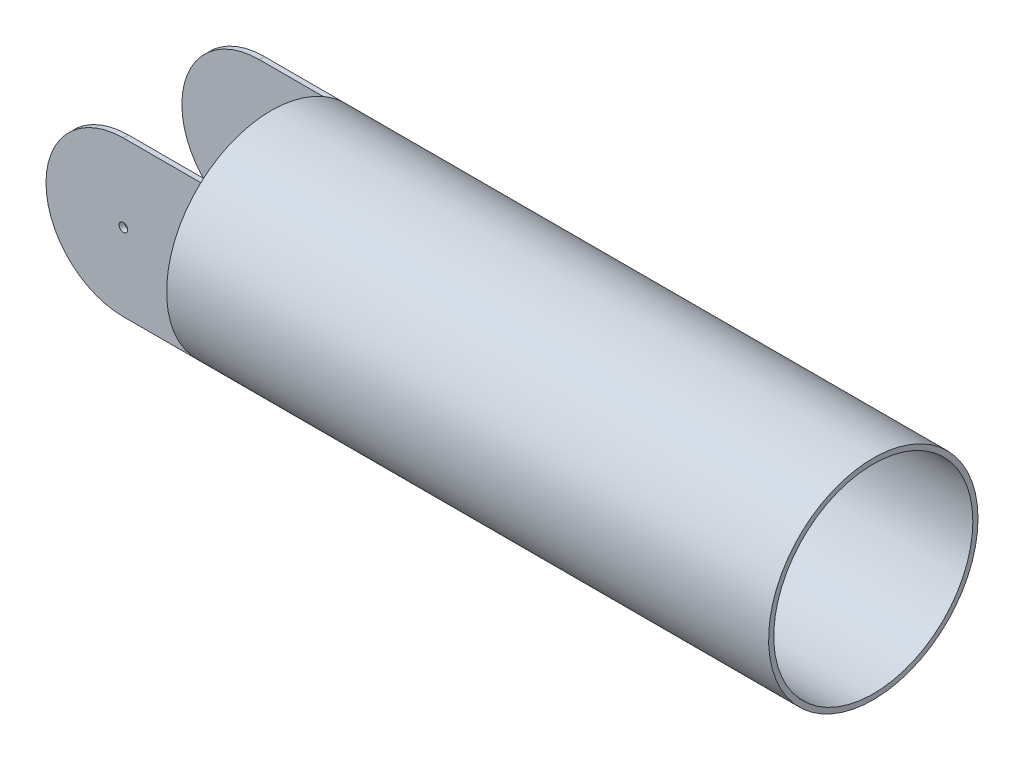
SolidWorks part; units mm, degrees
ref_plane "Ön Düzlem" through (0, 0, 0) normal (0, 0, 1) x (1, 0, 0)
ref_plane "Üst Düzlem" through (0, 0, 0) normal (0, 1, 0) x (1, 0, 0)
ref_plane "Sağ Düzlem" through (0, 0, 0) normal (1, 0, 0) x (0, 0, -1)
sketch "Çizim1" plane through (0, 0, 0) normal (0, 0, 1) x (1, 0, 0)
  line L1 (0, 0) -> (180, 0)
  line L2 (0, 0) -> (0, 180)
  line L3 (0, 180) -> (180, 180)
  line L4 (180, 0) -> (180, 180)
  dimension "D1" = 180
  dimension "D2" = 180
extrude "Yükseklik-Ekstrüzyon1" add sketch "Çizim1" along normal blind 164
sketch "Çizim3" plane through (180, 0, 0) normal (1, 0, 0) x (0, 0, -1)
  circle A0 centre (-82, 90) radius 121.7539
extrude "Yükseklik-Ekstrüzyon2" add sketch "Çizim3" along normal blind 700
sketch "Çizim4" plane through (0, 0, 164) normal (0, 0, 1) x (1, 0, 0)
  line L0 (90, 180) -> (0, 180)
  line L1 (0, 180) -> (0, 0)
  line L2 (0, 0) -> (90, 0)
  circle A0 centre (90, 90) radius 90
  line M1 (0, 180) -> (0, 0)
  line M2 (0, 0) -> (180, 0)
  line M4 (180, 180) -> (0, 180)
extrude "Kes-Ekstrüzyon1" cut sketch "Çizim4" against normal blind 700 contours A0 M4 M1 | A0 L1 M2
sketch "Çizim5" plane through (0, 180, 0) normal (0, 1, 0) x (1, 0, 0)
  line L0 (180, 0) -> (180, -164) construction
  line L1 (180, -6) -> (0, -6)
  line L2 (180, -6) -> (180, -158)
  line L3 (180, -158) -> (0, -158)
  line L4 (0, -6) -> (0, -158)
  line L5 (0, 0) -> (0, -164) construction
  line L6 (180, 0) -> (90, 0) construction
  line L7 (180, -164) -> (90, -164) construction
  dimension "D1" = 6
  dimension "D2" = 6
extrude "Kes-Ekstrüzyon2" cut sketch "Çizim5" against normal blind 700
sketch "Çizim6" plane through (0, 0, 164) normal (0, 0, 1) x (1, 0, 0)
  circle A0 centre (90, 90) radius 5
  dimension "D1" = 10
extrude "Kes-Ekstrüzyon3" cut sketch "Çizim6" against normal blind 700
sketch "Çizim7" plane through (880, 0, 0) normal (1, 0, 0) x (0, 0, -1)
  circle A0 centre (-82, 90) radius 115.7539
  circle A1 centre (-82, 90) radius 121.7539 construction
  dimension "D1" = 6
extrude "Kes-Ekstrüzyon4" cut sketch "Çizim7" against normal blind 694
